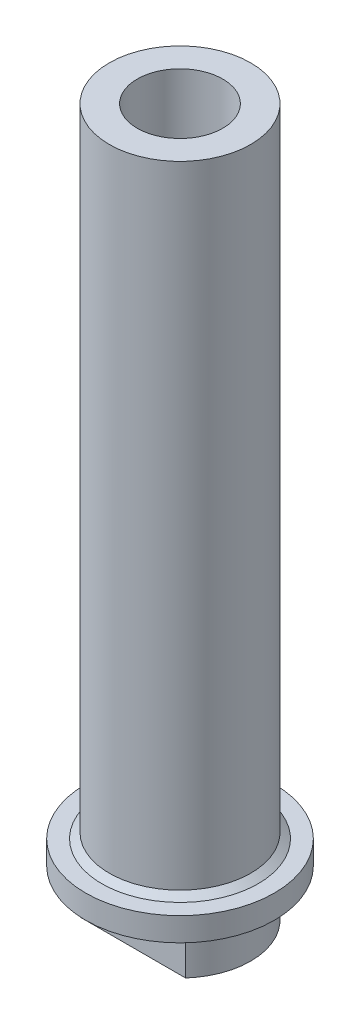
SolidWorks part; units mm, degrees
material "6061-T6 (SS)"
ref_plane "Front Plane" through (0, 0, 0) normal (0, 0, 1) x (1, 0, 0)
ref_plane "Top Plane" through (0, 0, 0) normal (0, 1, 0) x (1, 0, 0)
ref_plane "Right Plane" through (0, 0, 0) normal (1, 0, 0) x (0, 0, -1)
sketch "Sketch1" plane through (0, 0, 0) normal (0, 1, 0) x (1, 0, 0)
  circle A0 centre (0, 0) radius 9.525
  circle A1 centre (0, 0) radius 3.175
  dimension "D1" = 19.05
  dimension "D2" = 6.35
extrude "Boss-Extrude1" add sketch "Sketch1" along normal blind 95.25
ref_plane "Plane1" through (0, 6.35, 0) normal (0, -1, 0) x (-1, 0, 0)
sketch "Sketch3" plane through (0, 6.35, 0) normal (0, -1, 0) x (-1, 0, 0)
  circle A0 centre (0, 0) radius 12.7
  circle A1 centre (0, 0) radius 9.525
  dimension "D1" = 25.4
  dimension "D2" = 19.05
extrude "Boss-Extrude2" add sketch "Sketch3" against normal blind 3.175
sketch "Sketch4" plane through (0, 95.25, 0) normal (0, 1, 0) x (1, 0, 0)
  circle A0 centre (0, 0) radius 6.35
extrude "Boss-Extrude3" add sketch "Sketch4" against normal blind 19.05
hole_wizard "Tap Drill for 1/2-20 Tap1" positions "Sketch6" profile "Sketch5" hole size "1/2-20" standard "ANSI Inch" end condition up to next
sketch "Sketch6" plane through (0, 95.25, 0) normal (0, 1, 0) x (1, 0, 0)
  point P0 (0, 0)
sketch "Sketch5" plane through (0, 95.25, 0) normal (1, 0, 0) x (0, 0, 1)
  line L0 (0, 0) -> (0, 19.05)
  line L1 (0, 19.05) -> (5.7544, 19.05)
  line L2 (5.7544, 19.05) -> (5.7544, 0)
  line L5 (5.7544, 0) -> (0, 0)
  line L11 (0, -6.35) -> (0, 107.95) construction
  dimension "Thru Hole Dia." = 11.5087
  dimension "Thru Hole Depth" = 19.05
chamfer "Chamfer1" distance 1 angle 36 1 edges at (0, 9.525, -9.525)
sketch "Sketch8" plane through (0, 0, 0) normal (0, -1, 0) x (1, 0, 0)
  line L0 (-7.62, 6.35) -> (8.569, 6.35)
  line L5 (-7.62, -6.35) -> (8.569, -6.35)
  line L8 (-7.62, 6.35) -> (-7.62, 13.9928)
  line L9 (-7.62, 13.9928) -> (8.569, 13.9928)
  line L10 (8.569, 6.35) -> (8.569, 13.9928)
  line L12 (-7.62, -6.35) -> (-7.62, -14.8649)
  line L13 (-7.62, -14.8649) -> (8.569, -14.8649)
  line L14 (8.569, -6.35) -> (8.569, -14.8649)
  point P0 (0, 0)
  dimension "D1" = 12.7
  dimension "D2" = 6.35
  dimension "D3" = 7.62
  dimension "D4" = 7.6428
  dimension "D5" = 16.189
extrude "Cut-Extrude1" cut sketch "Sketch8" against normal up to surface (6.35 mm away) up to face at (0, 6.35, -9.525)
